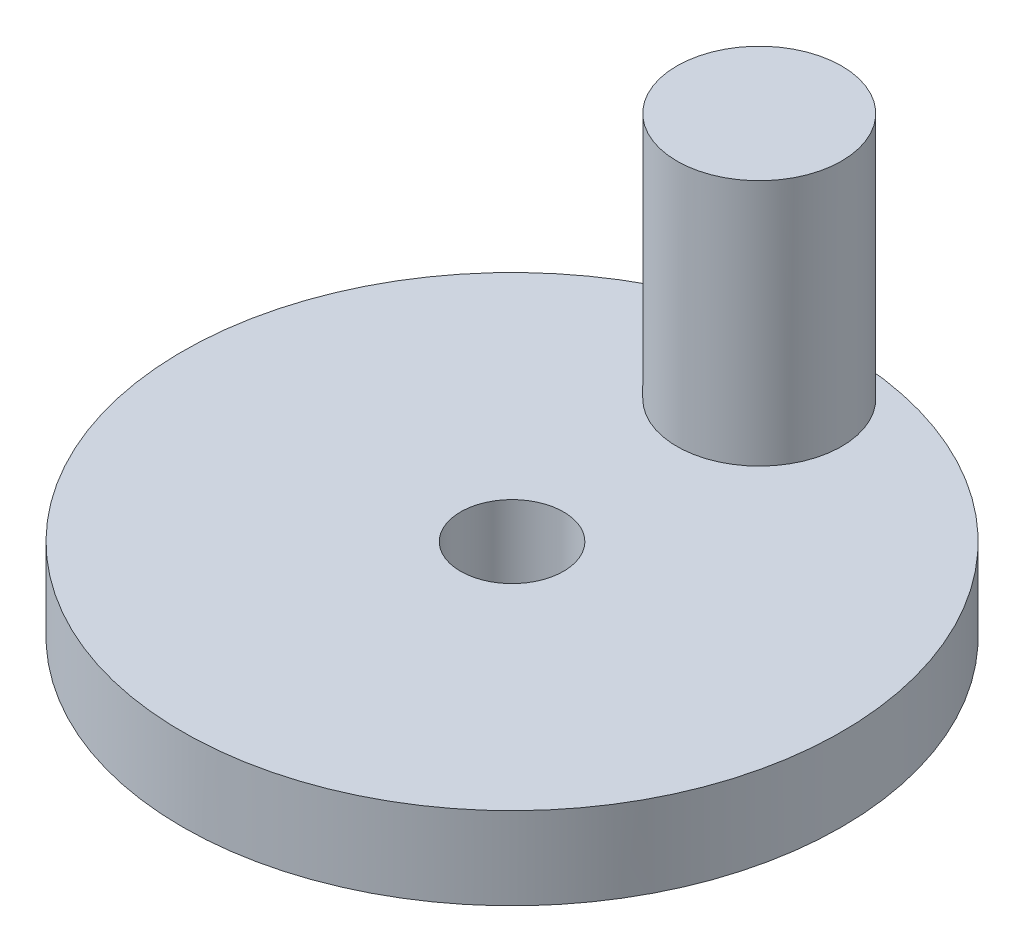
SolidWorks part; units mm, degrees
ref_plane "前视基准面" through (0, 0, 0) normal (0, 0, 1) x (1, 0, 0)
ref_plane "上视基准面" through (0, 0, 0) normal (0, 1, 0) x (1, 0, 0)
ref_plane "右视基准面" through (0, 0, 0) normal (1, 0, 0) x (0, 0, -1)
other "Configuration Table"
sketch "草图1" plane through (0, 0, 0) normal (0, 1, 0) x (1, 0, 0)
  circle A0 centre (0, 0) radius 1.25
  circle A1 centre (0, 0) radius 8
  dimension "D1" = 2.5
  dimension "D2" = 16
extrude "凸台-拉伸1" add sketch "草图1" along normal blind 2
sketch "草图3" plane through (0, 2, 0) normal (0, 1, 0) x (1, 0, 0)
  line L0 (0, 6) -> (0, 0) construction
  circle A0 centre (0, 6) radius 2
  circle A1 centre (0, 0) radius 8 construction
  dimension "D1" = 4
extrude "凸台-拉伸2" add sketch "草图3" along normal blind 6
